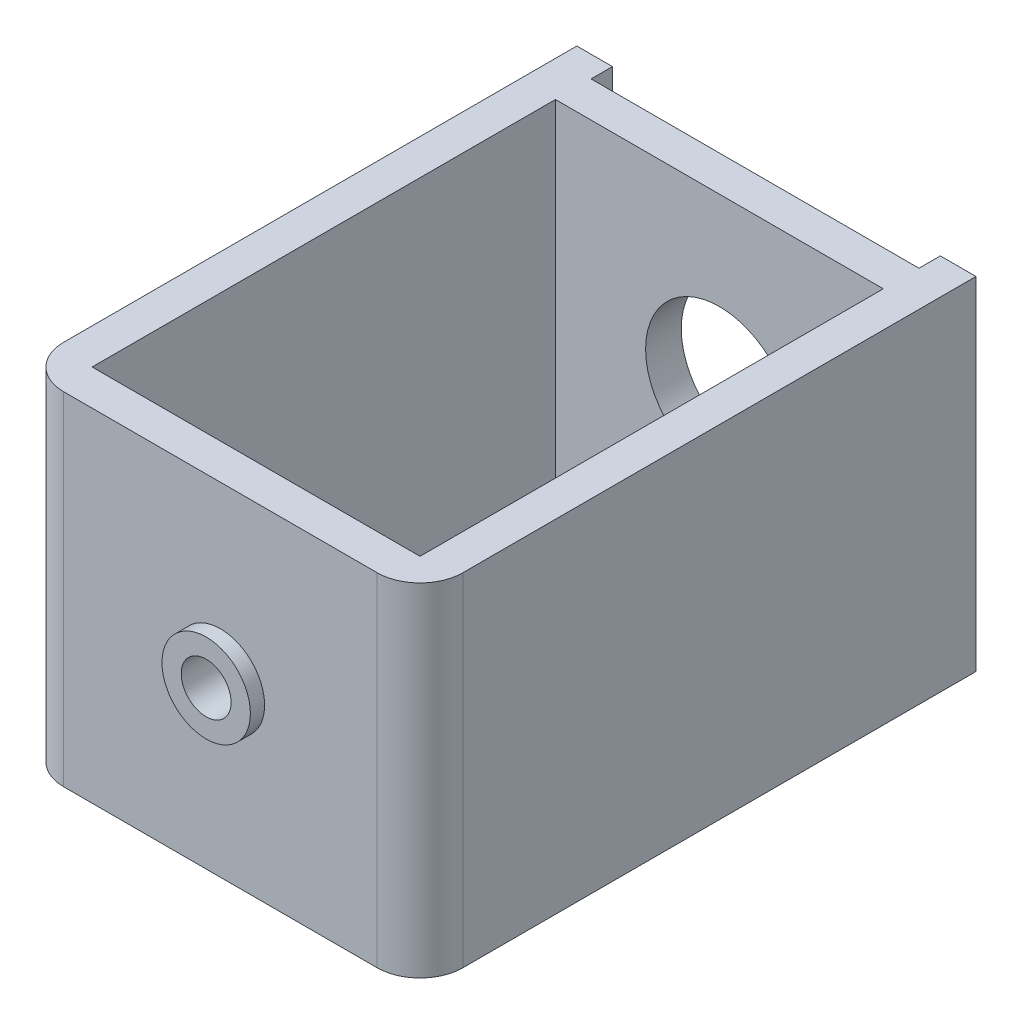
SolidWorks part; units mm, degrees
ref_plane "Front Plane" through (0, 0, 0) normal (0, 0, 1) x (1, 0, 0)
ref_plane "Top Plane" through (0, 0, 0) normal (0, 1, 0) x (1, 0, 0)
ref_plane "Right Plane" through (0, 0, 0) normal (1, 0, 0) x (0, 0, -1)
sketch "Sketch1" plane through (0, 0, 0) normal (0, 0, 1) x (1, 0, 0)
  line L1 (0, 0) -> (28, 0)
  line L2 (0, 0) -> (0, 24)
  line L3 (0, 24) -> (28, 24)
  line L4 (28, 0) -> (28, 24)
  dimension "D1" = 28
  dimension "D2" = 24
extrude "Boss-Extrude1" add sketch "Sketch1" along normal blind 39
sketch "Sketch2" plane through (0, 24, 0) normal (0, 1, 0) x (1, 0, 0)
  line L0 (0, -39) -> (0, 0) construction
  line L1 (2.5, -4) -> (25.5, -4)
  line L2 (2.5, -4) -> (2.5, -36.5)
  line L3 (2.5, -36.5) -> (25.5, -36.5)
  line L4 (25.5, -4) -> (25.5, -36.5)
  line L5 (28, -39) -> (28, 0) construction
  line L6 (28, -39) -> (0, -39) construction
  line L7 (28, 0) -> (0, 0) construction
  line L9 (2.5, 0) -> (25.5, 0)
  line L10 (2.5, 0) -> (2.5, -1.5)
  line L11 (2.5, -1.5) -> (25.5, -1.5)
  line L12 (25.5, 0) -> (25.5, -1.5)
  dimension "D1" = 2.5
  dimension "D2" = 2.5
  dimension "D3" = 2.5
  dimension "D4" = 4
  dimension "D5" = 1.5
extrude "Cut-Extrude1" cut sketch "Sketch2" against normal through all
sketch "Sketch3" plane through (0, 0, 0) normal (0, 0, -1) x (-1, 0, 0)
  line L0 (-28, 0) -> (-28, 24) construction
  line L2 (0, 0) -> (-2.5, 0) construction
  circle A0 centre (-14, 12) radius 5.175
  dimension "D1" = 10.35
  dimension "D2" = 14
  dimension "D3" = 12
extrude "Cut-Extrude2" cut sketch "Sketch3" against normal up to next
sketch "Sketch4" plane through (0, 0, 39) normal (0, 0, 1) x (1, 0, 0)
  line L0 (0, 24) -> (0, 0) construction
  line L1 (0, 0) -> (28, 0) construction
  circle A0 centre (14, 12) radius 1.75
  dimension "D1" = 3.5
  dimension "D2" = 14
  dimension "D3" = 12
extrude "Cut-Extrude3" cut sketch "Sketch4" against normal up to next
fillet "Fillet1" radius 3 2 edges at (0, 12, 39) (28, 12, 39)
sketch "Sketch5" plane through (0, 0, 39) normal (0, 0, 1) x (1, 0, 0)
  circle A0 centre (14, 12) radius 3.1
  circle M2 centre (14, 12) radius 1.75
  dimension "D1" = 6.2
extrude "Boss-Extrude2" add sketch "Sketch5" along normal blind 1 contours A0 M2
